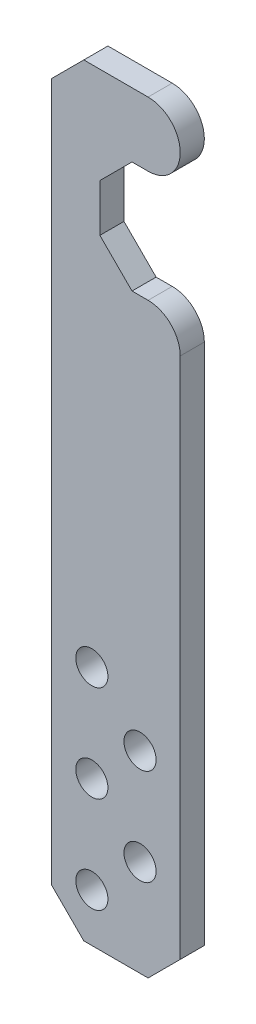
SolidWorks part; units mm, degrees
material "3003 Alloy"
ref_plane "Front Plane" through (0, 0, 0) normal (0, 0, 1) x (1, 0, 0)
ref_plane "Top Plane" through (0, 0, 0) normal (0, 1, 0) x (1, 0, 0)
ref_plane "Right Plane" through (0, 0, 0) normal (1, 0, 0) x (0, 0, -1)
sketch "Sketch1" plane through (0, 0, 0) normal (0, 0, 1) x (1, 0, 0)
  line L0 (0, 0) -> (0, -50) construction
  line L1 (0, -50) -> (-4, -54) construction
  line L2 (-4, -54) -> (-4, -100) construction
  line L3 (-4, -100) -> (4, -100)
  line L4 (4, -100) -> (4, 0) construction
  line L5 (4, 0) -> (0, 0) construction
  line L6 (2, -56.5228) -> (-1, -56.5228)
  line L7 (-1, -56.5228) -> (-1, -63.4772)
  line L8 (-1, -63.4772) -> (2, -63.4772)
  line L9 (2, -52.5228) -> (-4, -52.5228)
  line L10 (-4, -52.5228) -> (-4, -100)
  line L11 (4, -65.4772) -> (4, -100)
  circle A0 centre (5.5, -60) radius 4.5 construction
  arc A1 (4, -65.4772) -> (2, -63.4772) centre (2, -65.4772) ccw
  arc A2 (2, -56.5228) -> (2, -52.5228) centre (2, -54.5228) ccw
  dimension "D6" = 9
  dimension "D9" = 4
  dimension "D1" = 4
  dimension "D2" = 100
  dimension "D3" = 135
  dimension "D4" = 50
  dimension "D5" = 8
  dimension "D7" = 60
  dimension "D8" = 5.5
  dimension "D10" = 3
extrude "Boss-Extrude1" add sketch "Sketch1" along normal blind 1.5
sketch "Sketch2" plane through (0, 0, 1.5) normal (0, 0, 1) x (1, 0, 0)
  line L0 (-4, -100) -> (4, -100) construction
  line L2 (-4, -52.5228) -> (-4, -100) construction
  circle A0 centre (-1.5, -97) radius 1
  circle A1 centre (1.5, -94) radius 1
  circle A2 centre (-1.5, -91) radius 1
  circle A3 centre (-1.5, -85) radius 1
  circle A4 centre (1.5, -88) radius 1
  dimension "D6" = 2
  dimension "D1" = 6
  dimension "D2" = 6
  dimension "D3" = 6
  dimension "D4" = 3
  dimension "D5" = 3
  dimension "D7" = 2.5
  dimension "D8" = 3
extrude "Cut-Extrude1" cut sketch "Sketch2" against normal blind 5
chamfer "Chamfer1" distance 2 angle 45 5 edges at (-4, -100, 0.75) (4, -100, 0.75) (-1, -63.4772, 0.75) (-1, -56.5228, 0.75) (-4, -52.5228, 0.75)
